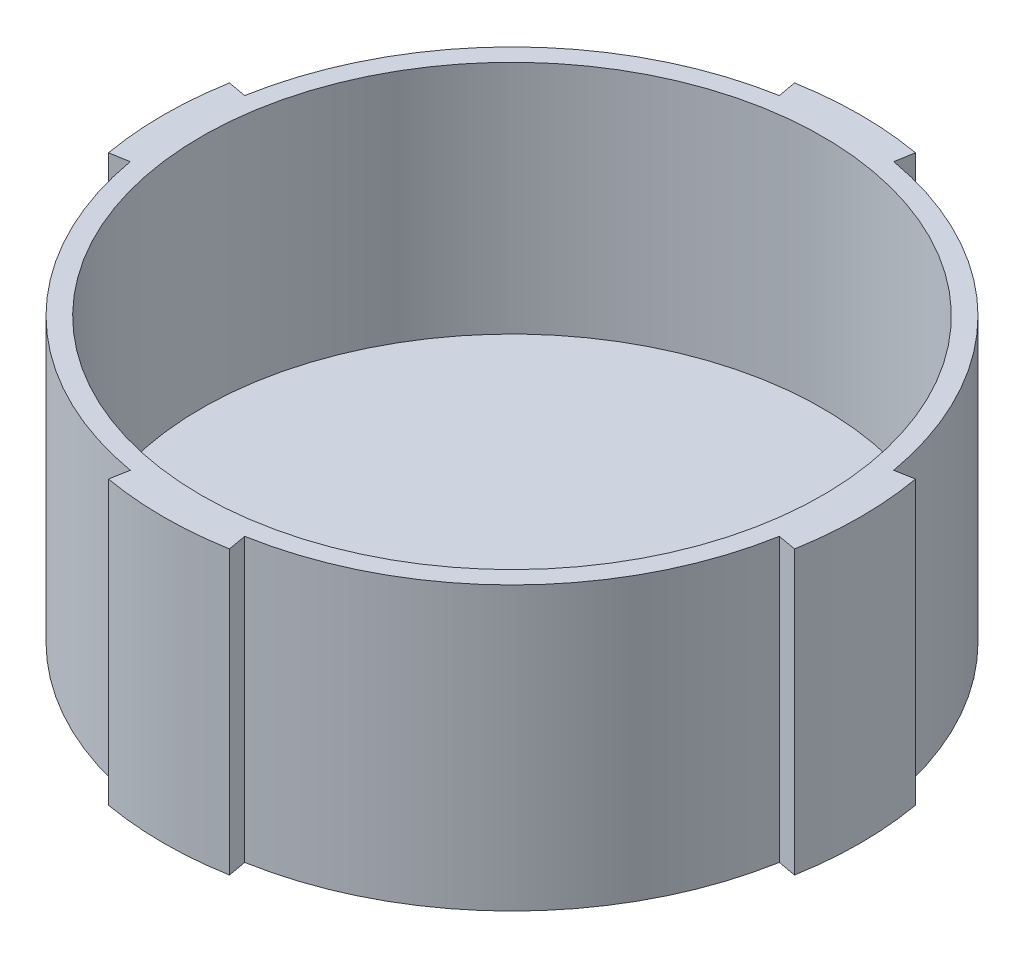
SolidWorks part; units mm, degrees
ref_plane "Front Plane" through (0, 0, 0) normal (0, 0, 1) x (1, 0, 0)
ref_plane "Top Plane" through (0, 0, 0) normal (0, 1, 0) x (1, 0, 0)
ref_plane "Right Plane" through (0, 0, 0) normal (1, 0, 0) x (0, 0, -1)
sketch "Sketch1" plane through (0, 0, 0) normal (0, 1, 0) x (1, 0, 0)
  circle A0 centre (0, 0) radius 37
  dimension "D1" = 74
extrude "Boss-Extrude1" add sketch "Sketch1" along normal blind 30
sketch "Sketch2" plane through (0, 30, 0) normal (0, 1, 0) x (1, 0, 0)
  line L0 (0, 0) -> (0, 37)
  line L1 (0, 0) -> (37, 0)
  line L2 (0, 0) -> (6.425, 36.4379)
  line L3 (0, 0) -> (36.4379, 6.425)
  line L4 (0, 0) -> (37, 0)
  line L5 (0, 0) -> (36.4379, -6.425)
  line L6 (0, 0) -> (0, -37)
  line L7 (0, 0) -> (-6.425, -36.4379)
  line L8 (0, 0) -> (-37, 0)
  line L9 (0, 0) -> (-36.4379, 6.425)
  line L10 (0, 0) -> (6.425, -36.4379)
  line L11 (0, 0) -> (-36.4379, -6.425)
  line L12 (0, 0) -> (-6.425, 36.4379)
  circle A0 centre (0, 0) radius 37 construction
  circle A1 centre (0, 0) radius 37
  circle A2 centre (0, 0) radius 35
  point P20 (0, 0)
  point P23 (0, 0)
  circle M7 centre (0, 0) radius 37
  dimension "D1" = 10
  dimension "D5" = 70
  dimension "D2" = 10
  dimension "D3" = 4
  dimension "D4" = 4
extrude "Cut-Extrude1" cut sketch "Sketch2" against normal blind 30 contours A2 L3 L2 M7 | A2 L12 L9 M7 | A2 L11 L7 M7 | A2 L10 L5 M7 | A1
sketch "Sketch3" plane through (0, 30, 0) normal (0, 1, 0) x (1, 0, 0)
  circle A0 centre (0, 0) radius 33
  dimension "D1" = 66
extrude "Cut-Extrude2" cut sketch "Sketch3" against normal blind 25
